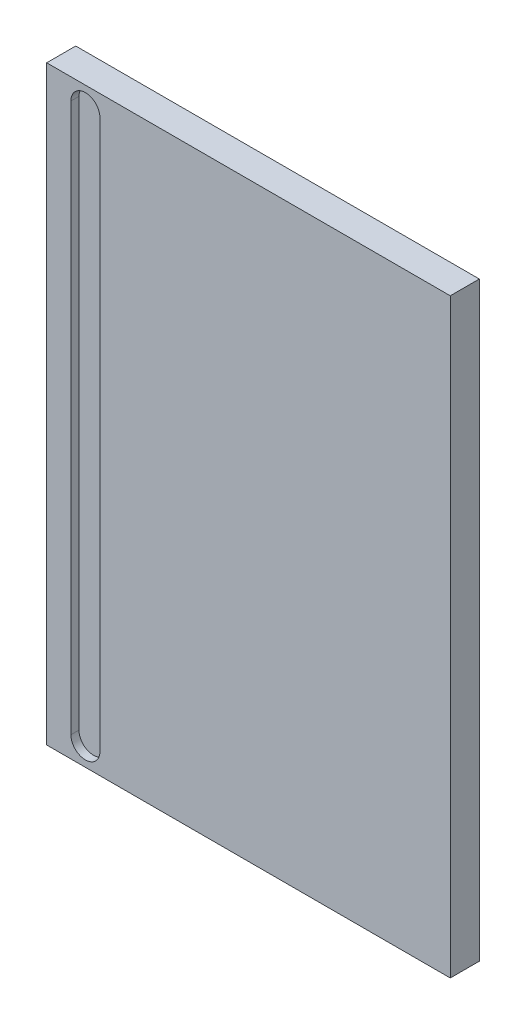
SolidWorks part; units mm, degrees
ref_plane "Спереди" through (0, 0, 0) normal (0, 0, 1) x (1, 0, 0)
ref_plane "Сверху" through (0, 0, 0) normal (0, 1, 0) x (1, 0, 0)
ref_plane "Справа" through (0, 0, 0) normal (1, 0, 0) x (0, 0, -1)
sketch "Эскиз1" plane through (0, 0, 0) normal (0, 0, 1) x (1, 0, 0)
  line L1 (125, -183) -> (-125, -183)
  line L2 (125, -183) -> (125, 183)
  line L3 (125, 183) -> (-125, 183)
  line L4 (-125, -183) -> (-125, 183)
  line L5 (125, -183) -> (-125, 183) construction
  line L6 (125, 183) -> (-125, -183) construction
  point P0 (0, 0)
  dimension "D1" = 366
  dimension "D2" = 250
extrude "Бобышка-Вытянуть1" add sketch "Эскиз1" along normal blind 18
sketch "Эскиз2" plane through (0, 0, 18) normal (0, 0, 1) x (1, 0, 0)
  line L0 (-125, 183) -> (-125, -183) construction
  line L2 (-110, 170) -> (-110, -170)
  line L4 (-92, 170) -> (-92, -170)
  line L5 (125, 183) -> (-125, 183) construction
  line L6 (-125, -183) -> (125, -183) construction
  arc A0 (-110, -170) -> (-92, -170) centre (-101, -170) ccw
  arc A1 (-92, 170) -> (-110, 170) centre (-101, 170) ccw
  dimension "D3" = 13
  dimension "D4" = 13
  dimension "D1" = 15
  dimension "D2" = 18
extrude "Вырез-Вытянуть1" cut sketch "Эскиз2" against normal blind 5
